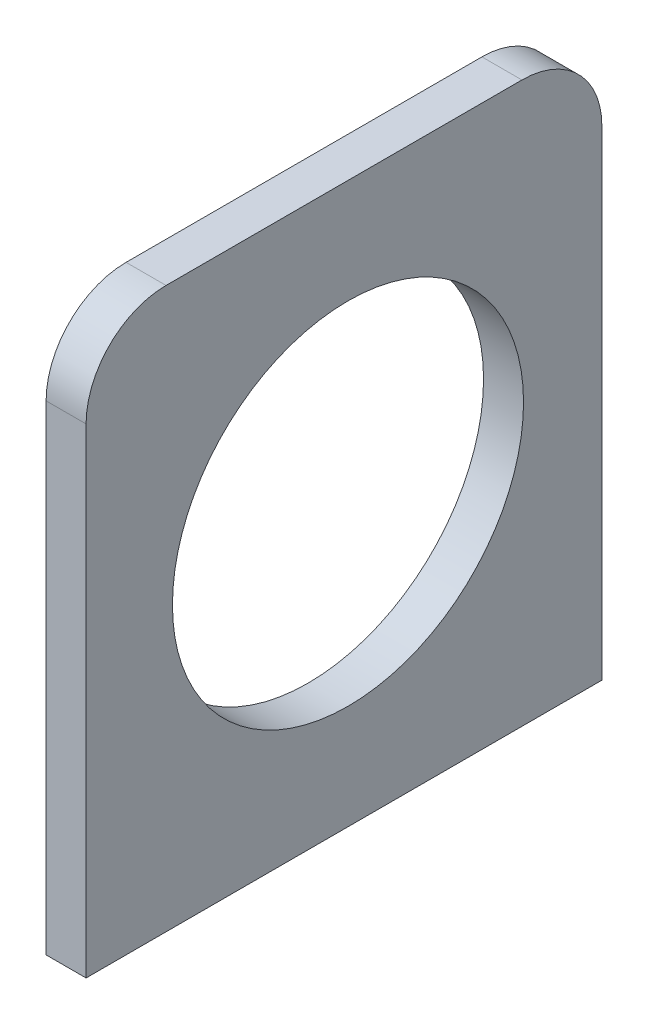
SolidWorks part; units mm, degrees
ref_plane "Front Plane" through (0, 0, 0) normal (0, 0, 1) x (1, 0, 0)
ref_plane "Top Plane" through (0, 0, 0) normal (0, 1, 0) x (1, 0, 0)
ref_plane "Right Plane" through (0, 0, 0) normal (1, 0, 0) x (0, 0, -1)
sketch "Sketch4" plane through (0, 0, 0) normal (0, 0, 1) x (1, 0, 0)
  line L0 (-2.7632, 7.1382) -> (2.2368, 7.1382)
  line L1 (2.2368, 7.1382) -> (2.2368, -62.8618)
  line L2 (2.2368, -62.8618) -> (-2.7632, -62.8618)
  line L3 (-2.7632, -62.8618) -> (-2.7632, 7.1382)
  dimension "D1" = 5
  dimension "D2" = 70
extrude "Boss-Extrude1" add sketch "Sketch4" along normal blind 64.5
fillet "Fillet3" radius 10 1 edges at (-0.2632, 7.1382, 64.5)
fillet "Fillet4" radius 10 1 edges at (-0.2632, 7.1382, 0)
sketch "Sketch5" plane through (-2.7632, 0, 0) normal (-1, 0, 0) x (0, 0, 1)
  line L3 (31.75, -27.8618) -> (64.5, -27.8618) construction
  line L4 (64.5, -2.8618) -> (64.5, -62.8618) construction
  circle A1 centre (31.75, -27.8618) radius 21.9509
  dimension "D1" = 32.75
extrude "Cut-Extrude1" cut sketch "Sketch5" against normal blind 10
